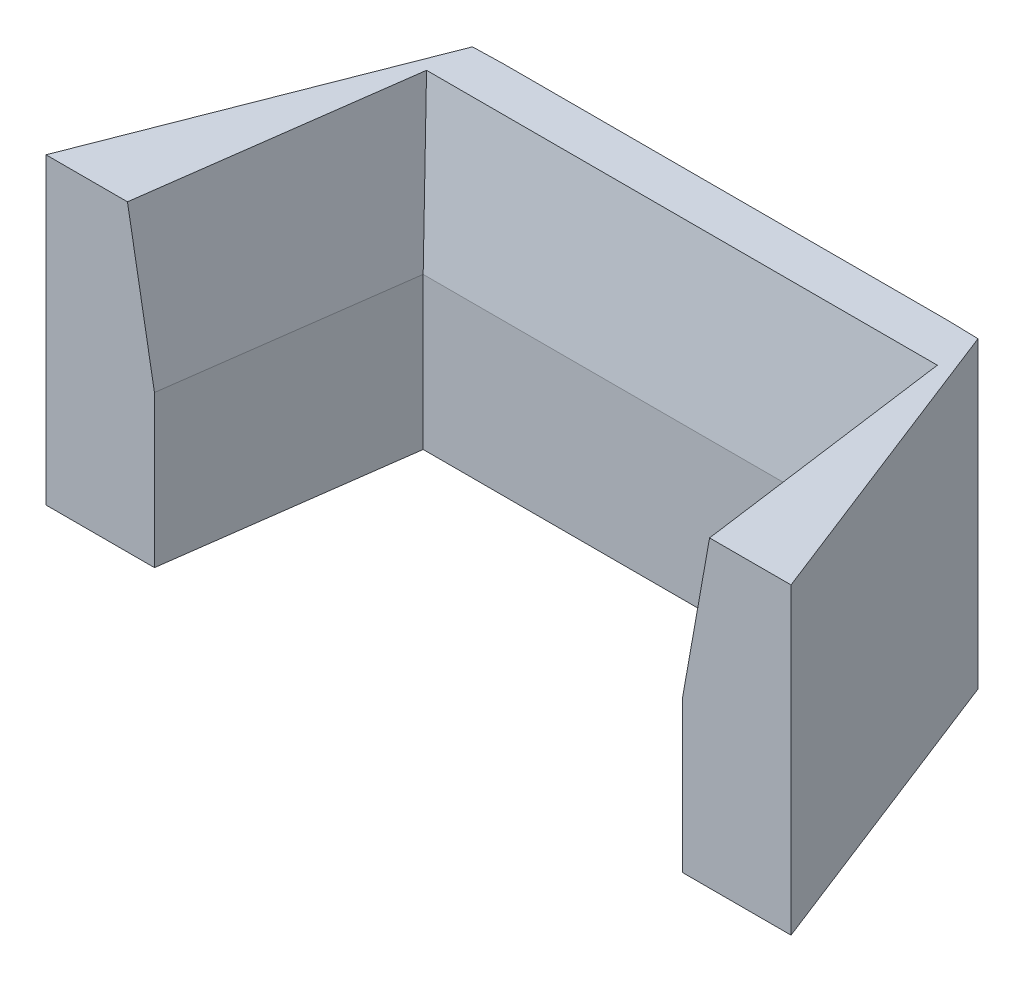
SolidWorks part; units mm, degrees
ref_plane "Front Plane" through (0, 0, 0) normal (0, 0, 1) x (1, 0, 0)
ref_plane "Top Plane" through (0, 0, 0) normal (0, 1, 0) x (1, 0, 0)
ref_plane "Right Plane" through (0, 0, 0) normal (1, 0, 0) x (0, 0, -1)
sketch "Croquis2" plane through (0, 0, 0) normal (0, 1, 0) x (1, 0, 0)
  line L0 (1.7931, 35.333) -> (-12, 0)
  line L1 (-12, 0) -> (0, 0)
  line L2 (0, 0) -> (4.7931, 35.4086)
  line L3 (4.7931, 35.4086) -> (1.7931, 35.333)
  line L4 (48.7931, 35.4086) -> (4.7931, 35.4086)
  line L5 (26.7931, 35.4086) -> (26.7931, 17.6731) construction
  line L6 (48.7931, 35.4086) -> (51.7931, 35.333)
  line L7 (53.5861, 0) -> (48.7931, 35.4086)
  line L8 (65.5861, 0) -> (53.5861, 0)
  line L9 (51.7931, 35.333) -> (65.5861, 0)
  line L10 (3.8455, 28.4086) -> (49.7406, 28.4086)
  dimension "D1" = 12
  dimension "D2" = 35.4086
  dimension "D3" = 35.333
  dimension "D4" = 68.676
  dimension "D5" = 3
  dimension "D6" = 50
  dimension "D7" = 7
extrude "Saliente-Extruir1" add sketch "Croquis2" along normal blind 30 contours L2 L3 L0 L1 | L5 L4 L2 L10 | L4 L5 L10 L7 | L9 L6 L7 L8
sketch "Croquis4" plane through (0, 0, 0) normal (1, 0, 0) x (0, 0, -1)
  line L0 (0, 0) -> (5, 0)
  line L1 (5, 0) -> (5, 30)
  line L2 (5, 30) -> (-4.9066, 30)
  line L3 (-4.9066, 30) -> (-4.9066, 0)
  line L4 (-4.9066, 0) -> (0, 0)
  dimension "D1" = 9.9066
  dimension "D2" = 5
  dimension "D3" = 30
extrude "Cortar-Extruir2" cut sketch "Croquis4" against normal mid plane 180
sketch "Croquis5" plane through (0, 0, 0) normal (0, -1, 0) x (-1, 0, 0)
  line L0 (-16.7931, 31.4086) -> (-36.7931, 31.4086)
  line L1 (-16.7931, 31.4086) -> (-16.7931, 33.4086)
  line L2 (-36.7931, 31.4086) -> (-36.7931, 33.4086)
  line L3 (-16.7931, 33.4086) -> (-36.7931, 33.4086)
  line L4 (-16.7931, 31.4086) -> (-36.7931, 33.4086) construction
  line L5 (-36.7931, 31.4086) -> (-16.7931, 33.4086) construction
  line L6 (-3.8455, 28.4086) -> (-3.8455, 35.3847) construction
  line L7 (-4.7931, 35.4086) -> (-1.7931, 35.333) construction
  line L8 (-3.8455, 28.4086) -> (-49.7406, 28.4086) construction
  line L9 (-48.7931, 35.4086) -> (-4.7931, 35.4086) construction
  point P1 (-26.7931, 32.4086)
  point P12 (-26.7931, 31.4086)
  point P15 (-26.7931, 28.4086)
  dimension "D1" = 2
  dimension "D2" = 20
  dimension "D3" = 2
extrude "Saliente-Extruir2" add sketch "Croquis5" along normal blind 3
chamfer "Chaflán1" distance 15 angle 10 3 edges at (51.3249, 30, -16.7043) (26.7931, 30, -28.4086) (2.2612, 30, -16.7043)
